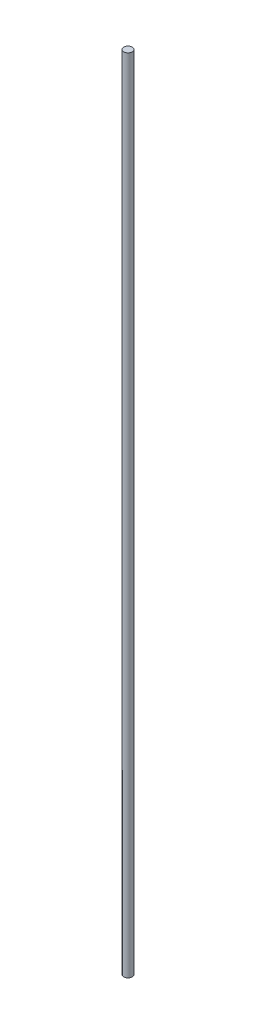
SolidWorks part; units mm, degrees
ref_plane "Front Plane" through (0, 0, 0) normal (0, 0, 1) x (1, 0, 0)
ref_plane "Top Plane" through (0, 0, 0) normal (0, 1, 0) x (1, 0, 0)
ref_plane "Right Plane" through (0, 0, 0) normal (1, 0, 0) x (0, 0, -1)
sketch "Sketch3" plane through (0, 0, 0) normal (0, 0, 1) x (1, 0, 0)
  line L0 (0, 0) -> (0, 95)
  point P4 (0, 0)
  dimension "D1" = 95
sketch "Sketch5" plane through (0, 0, 0) normal (0, 1, 0) x (1, 0, 0)
  circle A0 centre (0, 0) radius 0.5
  dimension "D1" = 1
sweep "Sweep1" add profiles "Sketch5" path "Sketch3"
